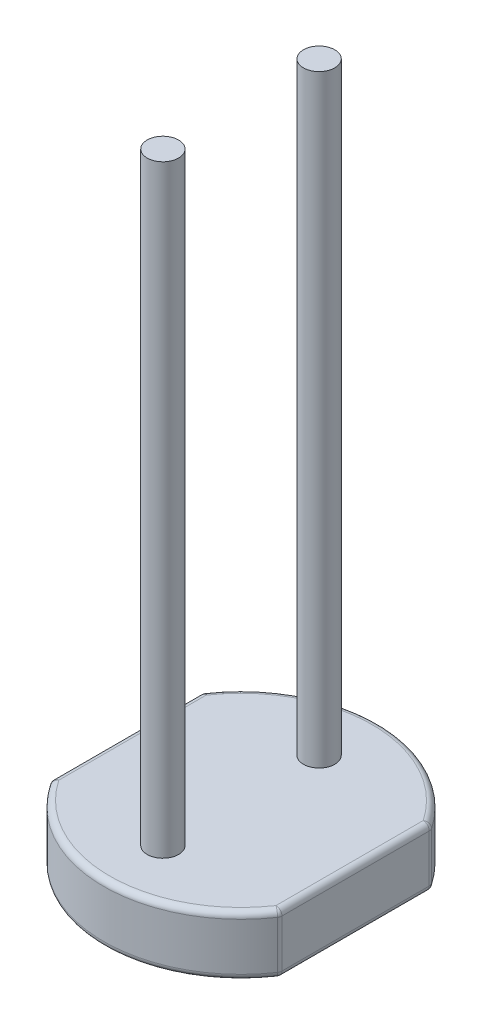
SolidWorks part; units mm, degrees
material "1060 Alloy"
ref_plane "Front Plane" through (0, 0, 0) normal (0, 0, 1) x (1, 0, 0)
ref_plane "Top Plane" through (0, 0, 0) normal (0, 1, 0) x (1, 0, 0)
ref_plane "Right Plane" through (0, 0, 0) normal (1, 0, 0) x (0, 0, -1)
sketch "Sketch1" plane through (0, 0, 0) normal (0, 1, 0) x (1, 0, 0)
  line L0 (-1.9, 1.2512) -> (-1.9, -1.2512)
  line L1 (1.9, 1.2512) -> (1.9, -1.2512)
  line L2 (-1.9, 1.2512) -> (1.9, 1.2512) construction
  line L3 (-1.9, -1.2512) -> (1.9, -1.2512) construction
  arc A0 (-1.9, -1.2512) -> (1.9, -1.2512) centre (0, 0) ccw
  arc A1 (1.9, 1.2512) -> (-1.9, 1.2512) centre (0, 0) ccw
  dimension "D1" = 4.55
  dimension "D2" = 3.8
extrude "Boss-Extrude1" add sketch "Sketch1" along normal blind 1
sketch "Sketch2" plane through (0, 1, 0) normal (0, 1, 0) x (1, 0, 0)
  line L0 (0, 0) -> (0, 1.295) construction
  line L1 (0, 0) -> (0, -1.295) construction
  circle A0 centre (0, 1.295) radius 0.26
  circle A1 centre (0, -1.295) radius 0.26
  dimension "D1" = 0.52
  dimension "D2" = 2.59
extrude "Boss-Extrude2" add sketch "Sketch2" along normal blind 10 and the other way blind 1.1
sketch "Sketch4" plane through (0, 0, 0) normal (0, -1, 0) x (1, 0, 0)
  line L0 (1.9, -1.2512) -> (1.9, 1.2512)
  line L1 (-1.9, 1.2512) -> (-1.9, -1.2512)
  line L2 (-1.4, 1.0912) -> (-1.4, -1.0912)
  line L3 (1.4, -1.0912) -> (1.4, 1.0912)
  line L4 (1.35, 1.1524) -> (1.35, -1)
  line L5 (1.05, -1) -> (1.05, 0.9)
  line L6 (0.75, 0.9) -> (0.75, -0.9)
  line L7 (0.45, -0.9) -> (0.45, 0.7)
  line L8 (0.15, 0.7) -> (0.15, -0.75)
  line L9 (0, 0) -> (0, -2.9017) construction
  line L10 (1.35, -1) -> (1.05, -1) construction
  line L11 (0, -0.9) -> (-0.3797, -0.9) construction
  line L12 (0.75, -0.9) -> (0.45, -0.9) construction
  line L13 (1.25, 1.1524) -> (1.25, -1)
  line L14 (1.15, -1) -> (1.15, 0.9)
  line L15 (0.65, 0.9) -> (0.65, -0.9)
  line L16 (0.55, -0.9) -> (0.55, 0.7)
  line L17 (0.05, 0.7) -> (0.05, -0.75)
  line L18 (1.25, 1.1524) -> (1.25, 1.2602)
  line L19 (-1.25, 1.1524) -> (-1.25, 1.2602)
  line L20 (-1.35, 1.1524) -> (-1.35, -1)
  line L21 (-1.25, 1.1524) -> (-1.25, -1)
  line L22 (-1.15, -1) -> (-1.15, 0.9)
  line L23 (-1.05, -1) -> (-1.05, 0.9)
  line L24 (-0.75, 0.9) -> (-0.75, -0.9)
  line L25 (-0.65, 0.9) -> (-0.65, -0.9)
  line L26 (-0.55, -0.9) -> (-0.55, 0.7)
  line L27 (-0.45, -0.9) -> (-0.45, 0.7)
  line L28 (-0.15, 0.7) -> (-0.15, -0.75)
  line L29 (-0.05, 0.7) -> (-0.05, -0.75)
  arc A0 (1.9, -1.2512) -> (-1.9, -1.2512) centre (0, 0) cw
  arc A1 (1.9, 1.2512) -> (-1.9, 1.2512) centre (0, 0) ccw
  arc A2 (-1.9, -1.2512) -> (1.9, -1.2512) centre (0, 0) ccw construction
  arc A3 (1.9, 1.2512) -> (-1.9, 1.2512) centre (0, 0) ccw construction
  arc A4 (1.4, -1.0912) -> (-1.4, -1.0912) centre (0, 0) cw
  arc A5 (1.4, 1.0912) -> (1.35, 1.1524) centre (0, 0) ccw
  arc A6 (1.35, -1) -> (1.05, -1) centre (1.2, -1) cw
  arc A7 (1.05, 0.9) -> (0.75, 0.9) centre (0.9, 0.9) ccw
  arc A8 (0.75, -0.9) -> (0.45, -0.9) centre (0.6, -0.9) cw
  arc A9 (0.45, 0.7) -> (0.15, 0.7) centre (0.3, 0.7) ccw
  arc A10 (0.15, -0.75) -> (-0.15, -0.75) centre (0, -0.75) cw
  arc A11 (1.25, -1) -> (1.15, -1) centre (1.2, -1) cw
  arc A12 (1.15, 0.9) -> (0.65, 0.9) centre (0.9, 0.9) ccw
  arc A13 (0.65, -0.9) -> (0.55, -0.9) centre (0.6, -0.9) cw
  arc A14 (0.55, 0.7) -> (0.05, 0.7) centre (0.3, 0.7) ccw
  arc A15 (0.05, -0.75) -> (0, -0.8) centre (0, -0.75) cw
  arc A16 (0.15, -0.75) -> (0, -0.9) centre (0, -0.75) cw construction
  arc A17 (1.25, 1.2602) -> (-1.25, 1.2602) centre (0, 0) ccw
  arc A18 (-1.25, -1) -> (-1.15, -1) centre (-1.2, -1) ccw
  arc A19 (1.4, 1.0912) -> (-1.4, 1.0912) centre (0, 0) ccw construction
  arc A20 (-1.35, -1) -> (-1.05, -1) centre (-1.2, -1) ccw
  arc A21 (-0.05, -0.75) -> (0, -0.8) centre (0, -0.75) ccw
  arc A22 (-0.65, -0.9) -> (-0.55, -0.9) centre (-0.6, -0.9) ccw
  arc A23 (-0.75, -0.9) -> (-0.45, -0.9) centre (-0.6, -0.9) ccw
  arc A24 (-1.05, 0.9) -> (-0.75, 0.9) centre (-0.9, 0.9) cw
  arc A25 (-1.15, 0.9) -> (-0.65, 0.9) centre (-0.9, 0.9) cw
  arc A26 (-0.55, 0.7) -> (-0.05, 0.7) centre (-0.3, 0.7) cw
  arc A27 (-0.45, 0.7) -> (-0.15, 0.7) centre (-0.3, 0.7) cw
  arc A28 (-1.35, 1.1524) -> (-1.4, 1.0912) centre (0, 0) ccw
  dimension "D2" = 0.3
  dimension "D4" = 0.1
  dimension "D5" = 0.8
  dimension "D6" = 1.45
  dimension "D7" = 1.6
  dimension "D8" = 1.8
  dimension "D9" = 1.9
  dimension "D1" = 0.5
  dimension "D3" = 0.1
extrude "Cut-Extrude1" cut sketch "Sketch4" against normal blind 0.01
fillet "Fillet1" radius 0.1 12 edges at (0, 1, 2.275) (-1.9, 1, 0) (-1.9, 0.505, 1.2512) (-1.9, 0.505, -1.2512) (1.9, 0.505, 1.2512) (1.9, 0.505, -1.2512) (-1.9, 0.01, 0) (0, 0.01, 2.275) (1.9, 0.01, 0) (0, 1, -2.275) (1.9, 1, 0) (0, 0.01, -2.275)
sketch "Sketch5" plane through (0, 11, 0) normal (0, 1, 0) x (1, 0, 0)
  circle A0 centre (0, 1.295) radius 0.26 construction
  point P0 (0.26, 1.295)
ref_plane "Plane1" through (1.9949, 0.3242, 0) normal (0.9871, 0.1604, 0) x (0, 0, -1)
